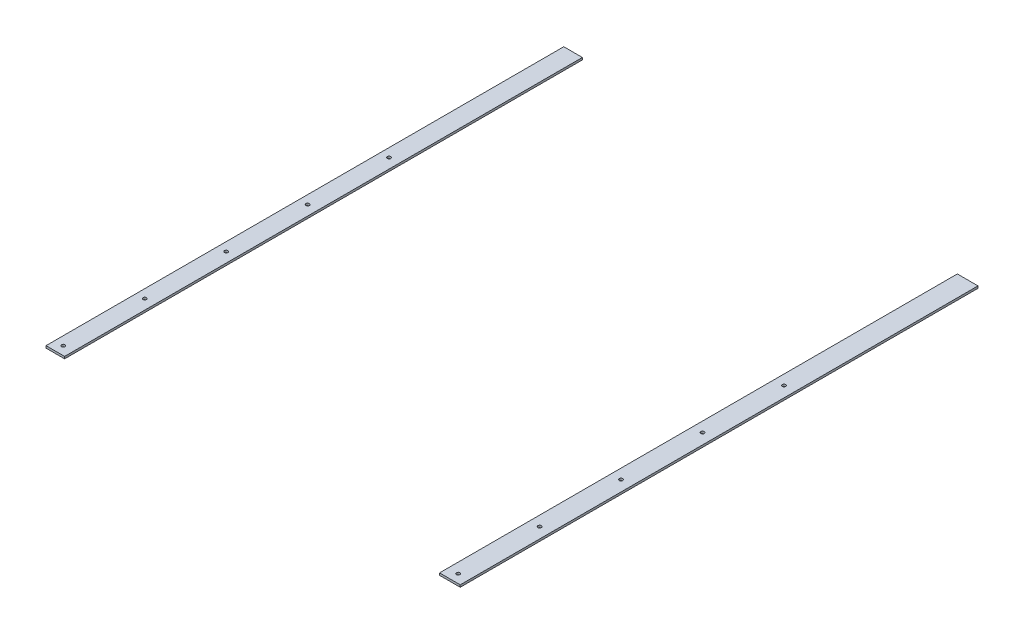
SolidWorks part; units mm, degrees
ref_plane "Front" through (0, 0, 0) normal (0, 0, 1) x (1, 0, 0)
ref_plane "Top" through (0, 0, 0) normal (0, 1, 0) x (1, 0, 0)
ref_plane "Right" through (0, 0, 0) normal (1, 0, 0) x (0, 0, -1)
sketch "Sketch1" plane through (0, 0, 0) normal (0, 1, 0) x (1, 0, 0)
  line L0 (0, 0) -> (0, 12.7) construction
  line L1 (0, 0) -> (609.6, 0)
  line L2 (0, 0) -> (0, 762)
  line L3 (0, 762) -> (609.6, 762)
  line L4 (609.6, 0) -> (609.6, 762)
  line L5 (0, 12.7) -> (12.7, 12.7) construction
  circle A1 centre (12.7, 12.7) radius 2.54
  circle A2 centre (593.852, 12.7) radius 2.54
  circle A3 centre (593.852, 132.588) radius 2.54
  circle A4 centre (593.852, 252.476) radius 2.54
  circle A5 centre (593.852, 372.364) radius 2.54
  circle A6 centre (593.852, 492.252) radius 2.54
  circle A7 centre (12.7, 132.588) radius 2.54
  circle A8 centre (12.7, 252.476) radius 2.54
  circle A9 centre (12.7, 372.364) radius 2.54
  circle A10 centre (12.7, 492.252) radius 2.54
  dimension "D1" = 762
  dimension "D5" = 5.08
  dimension "D2" = 609.6
  dimension "D3" = 12.7
  dimension "D4" = 12.7
  dimension "D6" = 2
  dimension "D7" = 5
extrude "Boss-Extrude1" add sketch "Sketch1" along normal blind 3.175
sketch "Sketch2" plane through (0, 3.175, 0) normal (0, 1, 0) x (1, 0, 0)
  line L0 (0, 0) -> (609.6, 0) construction
  line L1 (27.3686, 0) -> (579.1834, 0)
  line L2 (27.3686, 0) -> (27.3686, 762)
  line L3 (27.3686, 762) -> (579.1834, 762)
  line L4 (579.1834, 0) -> (579.1834, 762)
  line L5 (27.3686, 0) -> (579.1834, 762) construction
  line L6 (27.3686, 762) -> (579.1834, 0) construction
  line L7 (609.6, 762) -> (0, 762) construction
  line L8 (593.852, 12.7) -> (579.1834, 12.7) construction
  line L9 (12.7, 12.7) -> (27.3686, 12.7) construction
  point P4 (303.276, 381)
  point P15 (0, 0)
extrude "Cut-Extrude1" cut sketch "Sketch2" against normal up to next
